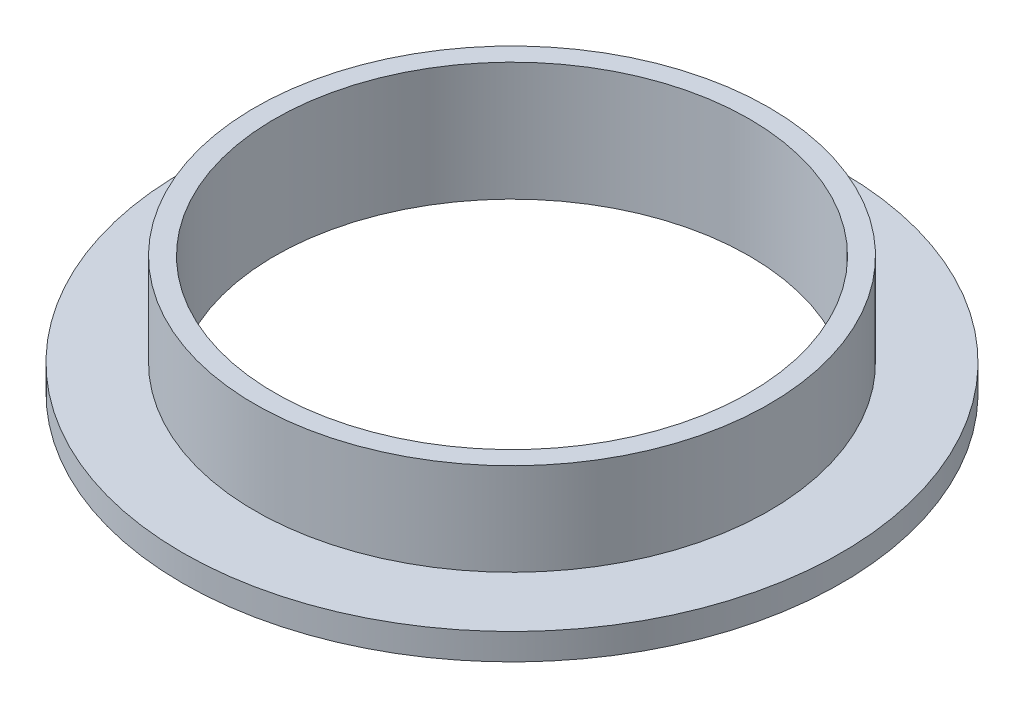
SolidWorks part; units mm, degrees
ref_plane "Front Plane" through (0, 0, 0) normal (0, 0, 1) x (1, 0, 0)
ref_plane "Top Plane" through (0, 0, 0) normal (0, 1, 0) x (1, 0, 0)
ref_plane "Right Plane" through (0, 0, 0) normal (1, 0, 0) x (0, 0, -1)
sketch "Sketch1" plane through (0, 0, 0) normal (0, 0, 1) x (1, 0, 0)
  line L0 (0, 0) -> (0, 12.1101) construction
  line L1 (18, 0) -> (25, 0)
  line L2 (25, 0) -> (25, 2)
  line L3 (25, 2) -> (19.5, 2)
  line L4 (19.5, 2) -> (19.5, 9)
  line L5 (19.5, 9) -> (18, 9)
  line L6 (18, 9) -> (18, 0)
  dimension "D1" = 39
  dimension "D2" = 39
  dimension "D3" = 7
  dimension "D4" = 2
  dimension "D5" = 50
  dimension "D6" = 36
revolve "Revolve1" add sketch "Sketch1" angle 360 about L0
